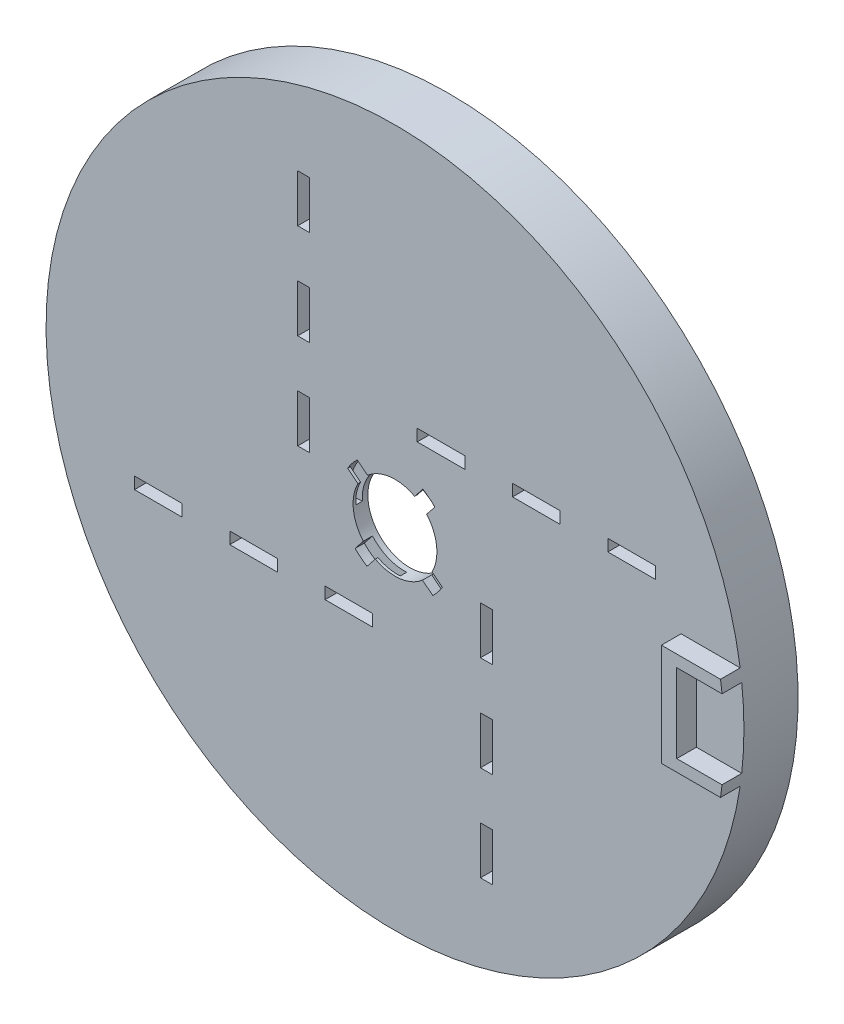
SolidWorks part; units mm, degrees
material "ABS"
ref_plane "Front Plane" through (0, 0, 0) normal (0, 0, 1) x (1, 0, 0)
ref_plane "Top Plane" through (0, 0, 0) normal (0, 1, 0) x (1, 0, 0)
ref_plane "Right Plane" through (0, 0, 0) normal (1, 0, 0) x (0, 0, -1)
sketch "Sketch1" plane through (0, 0, 0) normal (0, 0, 1) x (1, 0, 0)
  line L0 (0, 0) -> (0, -100) construction
  line L1 (-100, -100) -> (100, -100)
  line L2 (-100, -100) -> (-100, 100)
  line L3 (100, -100) -> (100, 100)
  line L4 (100, 100) -> (-100, 100)
  circle A0 centre (0, 0) radius 10.65
  point P7 (0, -100)
  dimension "D1" = 21.3
  dimension "D2" = 100
  dimension "D3" = 200
  dimension "D4" = 200
extrude "Boss-Extrude1" add sketch "Sketch1" against normal blind 3.75
sketch "Sketch2" plane through (0, 0, 0) normal (0, 0, 1) x (1, 0, 0)
  line L0 (0, 0) -> (0, 13.95) construction
  line L1 (0, 10.65) -> (0, 13.95)
  line L2 (8.6829, 10.9183) -> (6.6289, 8.3355)
  line L3 (-0.8501, 13.9241) -> (-0.649, 10.6302)
  circle A0 centre (0, 0) radius 10.65 construction
  circle A1 centre (0, 0) radius 13.95
  circle A2 centre (0, 0) radius 10.65
  arc A3 (0, 12.3) -> (-0.7495, 12.2771) centre (0, 0) ccw construction
  arc A4 (0, 12.3) -> (0.7495, 12.2771) centre (0, 0) cw construction
  arc A5 (0.7495, 12.2771) -> (7.6559, 9.6269) centre (0, 0) cw construction
  arc A6 (0.8501, 13.9241) -> (8.6829, 10.9183) centre (0, 0) cw
  arc A7 (0, 13.95) -> (0.8501, 13.9241) centre (0, 0) cw
  arc A8 (0, 13.95) -> (-0.8501, 13.9241) centre (0, 0) ccw
  arc A9 (0.649, 10.6302) -> (6.6289, 8.3355) centre (0, 0) cw
  arc A10 (0, 10.65) -> (0.649, 10.6302) centre (0, 0) cw
  arc A11 (0, 10.65) -> (-0.649, 10.6302) centre (0, 0) ccw
  dimension "D7" = 21.3
  dimension "D2" = 0.75
  dimension "D3" = 0.75
  dimension "D4" = 35
  dimension "D1" = 3.3
  dimension "D5" = 1.65
  dimension "D6" = 1.65
extrude "Cut-Extrude4" cut sketch "Sketch2" against normal mid plane 1.65 from offset 1.5 contours L2 A9 A10 A11 L3 A8 A7 A6 offset against normal yes
sketch "Sketch4" plane through (0, 0, -2.325) normal (0, 0, 1) x (1, 0, 0)
  line L0 (5.0003, 9.4031) -> (7.0769, 12.0216)
  line L1 (8.0358, 6.9892) -> (10.1194, 9.6021)
  arc A0 (6.6289, 8.3355) -> (8.0358, 6.9892) centre (0, 0) cw
  arc A1 (6.6289, 8.3355) -> (5.0003, 9.4031) centre (0, 0) ccw
  arc A2 (8.6829, 10.9183) -> (7.0769, 12.0216) centre (0, 0) ccw
  arc A3 (8.6829, 10.9183) -> (10.1194, 9.6021) centre (0, 0) cw
  dimension "D1" = 1.95
  dimension "D2" = 1.95
  dimension "D3" = 1.95
  dimension "D4" = 1.95
extrude "Cut-Extrude5" cut sketch "Sketch4" along normal through all
pattern_circular "CirPattern1" count 4 over 360 about axis through (0, 0, 0) along (0, 0, 1) of "Cut-Extrude5", "Cut-Extrude4"
sketch "Sketch5" plane through (0, 0, 0) normal (0, 0, 1) x (1, 0, 0)
  line L0 (0, 0) -> (15, 0)
  line L1 (15, 0) -> (47, 0)
  line L2 (47, 0) -> (15.5, 0)
  line L3 (15.5, 0) -> (5.65, 0)
  line L4 (5.65, 0) -> (5.65, 21.7)
  line L5 (5.65, 21.7) -> (17.75, 21.7)
  line L6 (5.65, 21.7) -> (5.65, 24.7)
  line L7 (17.75, 21.7) -> (17.75, 24.7)
  line L8 (5.65, 24.7) -> (17.75, 24.7)
  line L9 (17.75, 21.7) -> (29.85, 21.7)
  line L10 (29.85, 21.7) -> (29.85, 24.7)
  line L11 (29.85, 21.7) -> (41.95, 21.7)
  line L12 (29.85, 24.7) -> (41.95, 24.7)
  line L13 (41.95, 21.7) -> (41.95, 24.7)
  line L14 (41.95, 21.7) -> (54.05, 21.7)
  line L15 (54.05, 21.7) -> (66.15, 21.7)
  line L16 (54.05, 21.7) -> (54.05, 24.7)
  line L17 (66.15, 21.7) -> (66.15, 24.7)
  line L18 (54.05, 24.7) -> (66.15, 24.7)
  dimension "D1" = 15
  dimension "D2" = 32
  dimension "D3" = 31.5
  dimension "D4" = 9.85
  dimension "D5" = 21.7
  dimension "D6" = 12.1
  dimension "D7" = 3
  dimension "D8" = 12.1
  dimension "D9" = 12.1
  dimension "D10" = 12.1
  dimension "D11" = 12.1
  dimension "D12" = 3
  dimension "D13" = 3
extrude "Cut-Extrude6" cut sketch "Sketch5" against normal blind 10 contours L11 L13 L12 L10 | L18 L16 L15 L17 | L5 L6 L8 L7
pattern_circular "CirPattern2" count 4 over 360 about axis through (0, 0, 0) along (0, 0, 1) of "Cut-Extrude6"
sketch "Sketch6" plane through (0, 0, -3.75) normal (0, 0, -1) x (-1, 0, 0)
  line L0 (100, -100) -> (-100, -100)
  line L1 (100, -100) -> (100, 100.1827)
  line L2 (-100, -100) -> (-100, 100.1827)
  line L3 (100, 100.1827) -> (-100, 100.1827)
  circle A0 centre (0, 0) radius 70.611 construction
  circle A1 centre (0, 0) radius 88.611
  dimension "D1" = 18
extrude "Cut-Extrude7" cut sketch "Sketch6" against normal through all contours L0 L1 L3 L2 | A1
sketch "Sketch8" plane through (0, 0, 0) normal (0, 0, 1) x (1, 0, 0)
  line L0 (0, 0) -> (-80.611, 0)
  line L1 (-88.2738, 7.723) -> (-86.7795, 7.5922)
  line L2 (-88.2738, -7.723) -> (-86.7795, -7.5922)
  circle A0 centre (0, 0) radius 88.611 construction
  circle A1 centre (0, 0) radius 87.111 construction
  circle A2 centre (0, 0) radius 86.111
  circle A3 centre (0, 0) radius 84.611
  arc A5 (-88.2738, 7.723) -> (-88.2738, -7.723) centre (0, 0) cw
  arc A6 (-88.2738, 7.723) -> (-88.2738, -7.723) centre (0, 0) ccw construction
  arc A7 (-86.7795, 7.5922) -> (-86.7795, -7.5922) centre (0, 0) cw
  circle A8 centre (0, 0) radius 88.611 construction
  dimension "D4" = 1.5
  dimension "D1" = 1.5
  dimension "D2" = 1
  dimension "D3" = 1.5
extrude "Boss-Extrude2" add sketch "Sketch8" against normal blind 13.75 contours A0 A1 | A2 A3 | L1 A7 L2 A5
sketch "Sketch9" plane through (0, 0, 0) normal (0, 0, 1) x (1, 0, 0)
  line L0 (0, 0) -> (88.611, 0)
  line L1 (0, 0) -> (83.2671, 30.3067) construction
  circle A0 centre (0, 0) radius 88.611 construction
  dimension "D1" = 20
ref_plane "Plane1" through (83.2671, 0, 0) normal (1, 0, 0) x (0, 0, -1)
sketch "Sketch10" plane through (83.2671, 0, 0) normal (1, 0, 0) x (0, 0, -1)
  line L0 (0, 30.3067) -> (3.75, 30.3067) construction
  circle A0 centre (1.875, 30.3067) radius 0.825
  dimension "D1" = 3.75
  dimension "D2" = 1.65
sketch "Sketch11" plane through (0, 0, 0) normal (0, 0, 1) x (1, 0, 0)
  line L0 (76.546, -10) -> (88.0449, -10)
  line L1 (76.546, -10) -> (88.0449, -10) construction
  line L2 (76.546, 10) -> (76.546, -10) construction
  line L3 (76.546, -10) -> (76.546, 10)
  line L4 (76.546, 10) -> (88.0449, 10)
  line L5 (88.611, 0) -> (0, 0) construction
  line L6 (106.546, -13) -> (87.6522, -13) construction
  line L7 (87.6522, 13) -> (72.6522, 13)
  line L8 (72.6522, 13) -> (72.6522, -13)
  line L9 (72.6522, -13) -> (87.6522, -13)
  arc A0 (88.0449, -10) -> (87.6522, -13) centre (0, 0) cw
  circle A1 centre (0, 0) radius 88.611 construction
  arc A4 (88.0449, 10) -> (87.6522, 13) centre (0, 0) ccw
  dimension "D1" = 15
extrude "Boss-Extrude3" add sketch "Sketch11" along normal blind 5
equation "\"OuterThickness\"= 3mm"
equation "\"MasterFillet\"= 3mm"
equation "\"PartSeperation\"= 6mm"
equation "\"Tolerance\"= 0.15mm"
equation "\"HeightPart\"= 100mm"
equation "\"Holes\"= 1.5mm"
equation "\"SpineHolderThickness\"= 3mm"
equation "\"SpineHolderDepth\" = 3mm"
equation "\"D1@Sketch1\"= \"SpineDiameter\" + \"SpineHolderThickness\" * 2 + \"Tolerance\" * 2"
equation "\"D3@Sketch1\"=\"HeightPart\"*2"
equation "\"D4@Sketch1\"=\"HeightPart\"*2"
equation "\"D1@Boss-Extrude1\"=\"SpineHolderDepth\"*1.25"
equation "\"D1@Sketch2\"=\"Tolerance\"*2+\"SpineHolderThickness\""
equation "\"D2@Sketch2\"=\"SpineHolderThickness\"/4"
equation "\"D3@Sketch2\"=\"SpineHolderThickness\"/4"
equation "\"D5@Sketch2\"=\"Tolerance\"+\"SpineHolderThickness\"/2"
equation "\"D19@Cut-Extrude4\"=\"SpineHolderDepth\"/2"
equation "\"D1@Cut-Extrude4\"=\"SpineHolderThickness\"/2+\"Tolerance\""
equation "\"D1@Sketch4\"=\"Tolerance\"*3+\"SpineHolderThickness\"/2"
equation "\"D2@Sketch4\"=\"Tolerance\"*3+\"SpineHolderThickness\"/2"
equation "\"D3@Sketch4\"=\"Tolerance\"*3+\"SpineHolderThickness\"/2"
equation "\"D4@Sketch4\"=\"Tolerance\"*3+\"SpineHolderThickness\"/2"
equation "\"D2@Sketch1\"=\"HeightPart\""
equation "\"MotorLength\" = 40.5mm"
equation "\"MotorWidth\" = 20.3mm"
equation "\"AttachmentHeight\"= 3mm"
equation "\"SpoolDiameter\"= 60mm"
equation "\"SpoolHeight\"= 2mm"
equation "\"SpoolRidgeHeight\"= 1mm"
equation "\"SpoolRidgeDepth\"= 2mm"
equation "\"SpoolSeperation\"= 2mm"
equation "\"ServoHolderWidthOffset\"= 20mm"
equation "\"MotorTransmitterToScrew\"= 21.7mm"
equation "\"SpoolToSpine\"= 15mm"
equation "\"D1@Sketch5\"=\"SpoolToSpine\""
equation "\"D2@Sketch5\"=\"SpoolDiameter\"/2+\"SpoolRidgeDepth\""
equation "\"SpoolCenterToMotor\" = 31.5mm"
equation "\"D3@Sketch5\"=\"SpoolCenterToMotor\""
equation "\"D4@Sketch5\"=((\"MotorLength\"+\"ServoHolderWidthOffset\")-(\"MotorLength\"+\"Tolerance\"*2))/2"
equation "\"D5@Sketch5\"=\"MotorTransmitterToScrew\""
equation "\"D6@Sketch5\"=(\"MotorLength\"+\"ServoHolderWidthOffset\")*1/5"
equation "\"D7@Sketch5\"=3"
equation "\"D8@Sketch5\"=(\"MotorLength\"+\"ServoHolderWidthOffset\")*1/5"
equation "\"D9@Sketch5\"=(\"MotorLength\"+\"ServoHolderWidthOffset\")*1/5"
equation "\"D10@Sketch5\"=(\"MotorLength\"+\"ServoHolderWidthOffset\")*1/5"
equation "\"D11@Sketch5\"=(\"MotorLength\"+\"ServoHolderWidthOffset\")*1/5"
equation "\"D12@Sketch5\"=3"
equation "\"D13@Sketch5\"=3"
equation "\"HubOffset\"= 18mm"
equation "\"D1@Sketch6\"=\"HubOffset\""
equation "\"D1@Boss-Extrude2\"=\"SpineHolderDepth\"*1.25+10.00mm"
equation "\"D1@Sketch10\"=\"SpineHolderDepth\"*1.25"
equation "\"D2@Sketch10\"=\"SpineHolderDepth\"/2 +\"Tolerance\""
equation "\"D6@Sketch2\"=\"Tolerance\"+\"SpineHolderThickness\"/2"
equation "\"D7@Sketch2\" = \"SpineDiameter\" + \"SpineHolderThickness\" * 2 + \"Tolerance\" * 2"
equation "\"DiscThickness\"= 4mm"
equation "\"LigamentThickness\"= 2mm"
equation "\"LigamentExtension\"= 1mm"
equation "\"LigamentAngle\"= 20deg"
equation "\"SpineDiameter\"= 15mm"
equation "\"LigamentDepth\"= 1mm"
equation "\"ServoFastenerHolders\"=2mm"
equation "\"ArduinoLength\" = 53.4mm"
equation "\"ArduinoWidth\" = 50mm"
equation "\"ArdYOffset\" = 29.5mm"
equation "\"ArdXOffset\" = 20.5mm"
equation "\"ArdXOffsetSmall\" = 25mm"
equation "\"MiddleServoOffset\"= 12mm"
equation "\"LargeServoOffset\"= 3mm"
equation "\"SmallServoOffset\"= 0mm"
equation "\"ToolHoleDiameter\"= 12mm"
